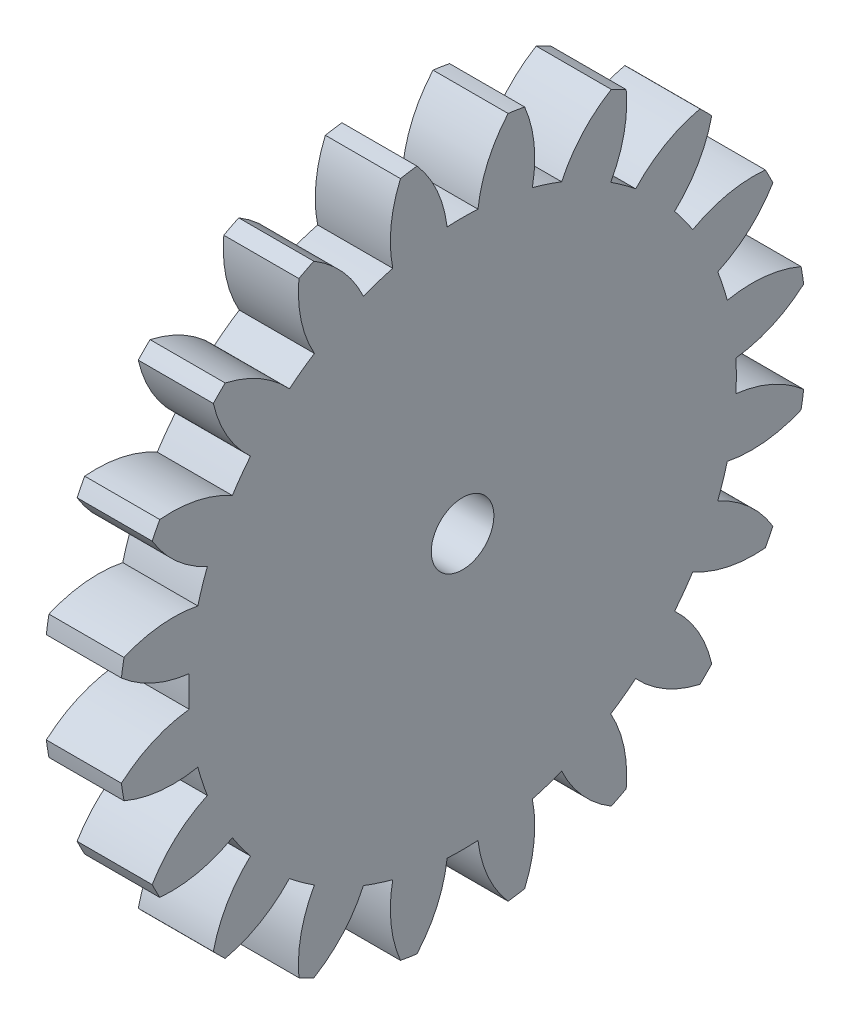
SolidWorks part; units mm, degrees
ref_plane "Plane1" through (0, 0, 0) normal (0, 0, 1) x (1, 0, 0)
ref_plane "Plane2" through (0, 0, 0) normal (0, 1, 0) x (1, 0, 0)
ref_plane "Plane3" through (0, 0, 0) normal (1, 0, 0) x (0, 0, -1)
sketch "HoldingSke" plane through (0, 0, 0) normal (0, 1, 0) x (1, 0, 0)
  line L0 (0, 0) -> (0.1879, -0.0684)
  line L1 (-15, 0) -> (100, 0) construction
  line L2 (0, 0) -> (-2.1039, 2.3779)
  line L3 (0, 0) -> (-11.863, 4.5341)
  line L4 (0, 0) -> (8.1152, 2.9537)
  line L5 (0, 0) -> (-46.8476, -17.4728)
  line L6 (0, 0) -> (-9.9476, -6.7116)
  line L7 (-2.1039, 2.3779) -> (8.6586, 51.2059)
  line L8 (-76.2, 54.61) -> (-74.4, 54.61)
  line L9 (-71.009, 38.7566) -> (-53.1078, 45.2721)
  line L10 (-76.2, 71.12) -> (104.1128, 71.12)
  line L11 (0, 0) -> (-12, 0)
  line L12 (-76.2, 101.6) -> (-76.033, 101.6)
  line L13 (24.9733, 27.94) -> (52.9518, 28.4284)
  line L14 (24.9733, 27.94) -> (24.9743, 27.94)
  line L15 (24.9733, 27.94) -> (100.4006, 29.5858)
  line L16 (-63.627, -5) -> (-12.827, -5)
  circle A0 centre (0, 0) radius 5
  circle A1 centre (0, 0) radius 37.5
  circle A2 centre (0, 0) radius 37.5
  circle A3 centre (0, 0) radius 5
  dimension "MHD" = 75
  dimension "Hub_dia" = 75
  dimension "Bore" = 10
  dimension "MBD" = 10
  dimension "Num_teeth" = 20
  dimension "Pitch_radius" = 180.3128
  dimension "Pitch" = 0.2
  dimension "Width" = 12
  dimension "Overall_len" = 50
  dimension "Show_teeth" = 20
  dimension "Thickness" = 12
  dimension "OAL" = 50.0001
  dimension "T_dim" = 1.8
  dimension "Ap" = 20
  dimension "H" = 19.05
  dimension "Backlash" = 0.167
  dimension "Addendum_fac" = 1
  dimension "Dedendum_fac" = 1.25
  dimension "Clearance_fac" = 0.25
  dimension "Dedendum_add" = 0.001
  dimension "Module" = 5
sketch "BasProSke" plane through (0, 0, 0) normal (0, 1, 0) x (1, 0, 0)
  line L0 (-10, 0) -> (60, 0) construction
  line L1 (0, 0) -> (0, 55)
  line L2 (0, 0) -> (12, 0)
  line L3 (12, 0) -> (12, 55)
  line L4 (12, 55) -> (0, 55)
  dimension "Diameter" = 110
  dimension "Thickness" = 12
revolve "Base-Revolve" add sketch "BasProSke" angle 360 about L0
sketch "TooCutSke" plane through (0, 0, 0) normal (1, 0, 0) x (0, 0, -1)
  line L1 (0, 0) -> (0, 107) construction
  line L2 (0, 0) -> (-4.2151, 49.822) construction
  line L3 (0, 0) -> (-15.6021, 98.5081) construction
  line L4 (-4.2151, 49.822) -> (-7.8011, 49.254) construction
  arc A0 (2.4648, 43.6795) -> (-2.4648, 43.6795) centre (0, 0) ccw
  arc A1 (7.3009, 54.5389) -> (-7.3009, 54.5389) centre (0, 0) ccw
  circle A2 centre (0, 0) radius 50 construction
  circle A3 centre (0, 0) radius 46.9846 construction
  arc A4 (-2.4648, 43.6795) -> (-7.3009, 54.5389) centre (-22.3276, 41.3405) ccw
  arc A5 (7.3009, 54.5389) -> (2.4648, 43.6795) centre (22.3276, 41.3405) ccw
  dimension "Root_dia" = 87.498
  dimension "Overcut_dia" = 110.0508
  dimension "Pitch_dia" = 100
  dimension "Base_dia" = 93.9693
  dimension "Flank_rad" = 20
  dimension "Half_ang" = 9
  dimension "Half_CT" = 3.6307
extrude "ToothCut" cut sketch "TooCutSke" along normal through all
fillet "Breaks" [suppressed] radius 0.1
fillet "RootFillets" [suppressed] radius 1.251
pattern_circular "TeethCuts" count 20 every 18 about axis through (-10, 0, 0) along (1, 0, 0) of "ToothCut", "RootFillets", "Breaks"
sketch "HubNeaOneSke" plane through (0, 0, 0) normal (-1, 0, 0) x (0, 0, 1)
  circle A0 centre (0, 0) radius 37.5
  dimension "Diameter" = 75
extrude "HubNearOne" [suppressed] add sketch "HubNeaOneSke" along normal blind 38.0001
sketch "HubNeaBotSke" plane through (0, 0, 0) normal (-1, 0, 0) x (0, 0, 1)
  circle A0 centre (0, 0) radius 37.5
  dimension "Diameter" = 75
extrude "HubNearBoth" [suppressed] add sketch "HubNeaBotSke" along normal blind 19
ref_plane "FarPln" through (12, 0, 0) normal (1, 0, 0) x (0, 0, -1)
sketch "HubFarSke" plane through (12, 0, 0) normal (1, 0, 0) x (0, 0, -1)
  circle A0 centre (0, 0) radius 37.5
  dimension "Diameter" = 75
extrude "HubFar" [suppressed] add sketch "HubFarSke" along normal blind 19
sketch "BorSke" plane through (0, 0, 0) normal (1, 0, 0) x (0, 0, -1)
  circle A0 centre (0, 0) radius 5
  dimension "Diameter" = 10
extrude "Bore" cut sketch "BorSke" along normal mid plane 100.0001
sketch "KeySke" plane through (0, 0, 0) normal (1, 0, 0) x (0, 0, -1)
  line L0 (-2, 0) -> (-2, 6.8)
  line L1 (-2, 6.8) -> (2, 6.8)
  line L2 (2, 6.8) -> (2, 0)
  line L3 (0, 0) -> (0, 34) construction
  line L4 (-2, 0) -> (2, 0)
  dimension "Offset" = 6.8
  dimension "Width" = 4
extrude "Keyway" [suppressed] cut sketch "KeySke" along normal mid plane 100.0001
pattern_circular "Keyway2" [suppressed] count 2 every 90 about axis through (-10, 0, 0) along (1, 0, 0)
equation "' \"Module@HoldingSke\" = 6.35"
equation "' \"Num_teeth@HoldingSke\" = 12"
equation "' \"Ap@HoldingSke\" =  20"
equation "' \"Width@HoldingSke\" = 0.5 * 25.4"
equation "' \"Hub_dia@HoldingSke\"= 1 * 25.4"
equation "' \"Overall_len@HoldingSke\" = 1.0 * 25.4"
equation "' \"Bore@HoldingSke\" = 0.75 * 25.4"
equation "' \"T_dim@HoldingSke\" = 0.1 * 25.4"
equation "' \"Width@KeySke\" = 0.25 * 25.4"
equation "' \"Show_teeth@HoldingSke\" = 13"
equation "' \"Backlash@HoldingSke\" = 0.009 * 25.4"
equation "' \"Addendum_fac@HoldingSke\" = 1.0"
equation "' \"Dedendum_fac@HoldingSke\" = 1.25"
equation "' \"Dedendum_add@HoldingSke\" = 0.00005 * 25.4"
equation "' \"Clearance_fac@HoldingSke\" = 0.25"
equation "\"Pitch@HoldingSke\" = 1 / \"Module@HoldingSke\""
equation "\"Overcut_dia@TooCutSke\" = (\"Num_teeth@HoldingSke\" + 2 * \"Addendum_fac@HoldingSke\") / \"Pitch@HoldingSke\" + 0.002 * 25.4"
equation "\"Pitch_dia@TooCutSke\" = \"Num_teeth@HoldingSke\" / \"Pitch@HoldingSke\""
equation "\"Base_dia@TooCutSke\" = \"Num_teeth@HoldingSke\" / \"Pitch@HoldingSke\" * cos((\"Ap@HoldingSke\"  * 3.14159265 / 180))"
equation "\"Root_dia@TooCutSke\" = (\"Num_teeth@HoldingSke\" + 2) / \"Pitch@HoldingSke\" - 2 * (\"Addendum_fac@HoldingSke\" + \"Dedendum_fac@HoldingSke\") / \"Pitch@HoldingSke\" - \"Dedendum_add@HoldingSke\" * 2"
equation "\"Half_ang@TooCutSke\" = 180 / \"Num_teeth@HoldingSke\""
equation "\"Half_CT@TooCutSke\" = \"Num_teeth@HoldingSke\" / \"Pitch@HoldingSke\" * sin((3.14159265 / 2 / \"Num_teeth@HoldingSke\")) / 2 - 7 * \"Backlash@HoldingSke\" / 4"
equation "\"Flank_rad@TooCutSke\" = \"Num_teeth@HoldingSke\" / \"Pitch@HoldingSke\" / 5"
equation "\"Radius@RootFillets\" = \"Clearance_fac@HoldingSke\" / \"Pitch@HoldingSke\" + \"Dedendum_add@HoldingSke\""
equation "\"Break_rad@Breaks\" = 0.02 / \"Pitch@HoldingSke\""
equation "\"Thickness@HoldingSke\" = \"Width@HoldingSke\""
equation "\"OAL@HoldingSke\" = \"Thickness@HoldingSke\""
equation "\"MHD@HoldingSke\" = (\"Num_teeth@HoldingSke\" + 2) / \"Pitch@HoldingSke\" - 2 * (\"Addendum_fac@HoldingSke\" + \"Dedendum_fac@HoldingSke\")  / \"Pitch@HoldingSke\" - \"Dedendum_add@HoldingSke\" * 2"
equation "\"MBD@HoldingSke\" = (\"Num_teeth@HoldingSke\" + 2) / \"Pitch@HoldingSke\" - 2 * (\"Addendum_fac@HoldingSke\" + \"Dedendum_fac@HoldingSke\")  / \"Pitch@HoldingSke\" - \"Dedendum_add@HoldingSke\" * 2 - 0.002 * 25.4"
equation "\"MHD@HoldingSke\" = ((sgn( \"MHD@HoldingSke\" - \"Hub_dia@HoldingSke\" )-1)*( \"MHD@HoldingSke\" - \"Hub_dia@HoldingSke\" ))/-2+ \"Hub_dia@HoldingSke\""
equation "\"MBD@HoldingSke\" = ((sgn( \"MBD@HoldingSke\" - \"Bore@HoldingSke\" )-1)*( \"MBD@HoldingSke\" - \"Bore@HoldingSke\" ))/-2+ \"Bore@HoldingSke\""
equation "\"OAL@HoldingSke\" = ((sgn( \"OAL@HoldingSke\" - \"Overall_len@HoldingSke\" )+1)*( \"OAL@HoldingSke\" - \"Overall_len@HoldingSke\" ))/2 + \"Overall_len@HoldingSke\" + 0.000002 * 25.4"
equation "\"Num_teeth@TeethCuts\" = int( \"Show_teeth@HoldingSke\" ) + 1"
equation "\"Num_teeth@TeethCuts\" = ((sgn( \"Num_teeth@TeethCuts\" - \"Num_teeth@HoldingSke\" )-1)*( \"Num_teeth@TeethCuts\" - \"Num_teeth@HoldingSke\" ))/-2+ \"Num_teeth@HoldingSke\""
equation "\"Num_teeth@TeethCuts\" = ((sgn( \"Num_teeth@TeethCuts\" - 2.0)+1)*( \"Num_teeth@TeethCuts\" - 2.0))/2 +2.0"
equation "\"Angle@TeethCuts\" = 360.0 / \"Num_teeth@HoldingSke\""
equation "\"Diameter@BasProSke\" = (\"Num_teeth@HoldingSke\" + 2 * \"Addendum_fac@HoldingSke\") / \"Pitch@HoldingSke\""
equation "\"Thickness@BasProSke\"  = \"Thickness@HoldingSke\""
equation "' \"Fillet_rad@BasProSke\" =  \"Thickness@HoldingSke\" * 0.05"
equation "\"MHD@HoldingSke\" = ((sgn( \"MHD@HoldingSke\" - \"Root_dia@TooCutSke\" )-1)*( \"MHD@HoldingSke\" - \"Root_dia@TooCutSke\" ))/-2+ \"Root_dia@TooCutSke\""
equation "\"Diameter@HubNeaOneSke\" = \"MHD@HoldingSke\""
equation "\"Length@HubNearOne\" = \"OAL@HoldingSke\" - \"Thickness@BasProSke\""
equation "\"Diameter@HubNeaBotSke\" = \"MHD@HoldingSke\""
equation "\"Length@HubNearBoth\" = ( \"OAL@HoldingSke\" - \"Thickness@BasProSke\" ) / 2.0"
equation "\"Thickness@FarPln\" = \"Thickness@BasProSke\""
equation "\"Diameter@HubFarSke\" = \"MHD@HoldingSke\""
equation "\"Length@HubFar\" = ( \"OAL@HoldingSke\" - \"Thickness@BasProSke\" ) / 2.0"
equation "\"Diameter@BorSke\" = \"MBD@HoldingSke\""
equation "\"D1@Bore\" = \"OAL@HoldingSke\" * 2.0"
equation "\"D1@Keyway\" = \"OAL@HoldingSke\" * 2.0"
equation "\"Offset@KeySke\" = \"T_dim@HoldingSke\" + \"MBD@HoldingSke\" / 2.0"
